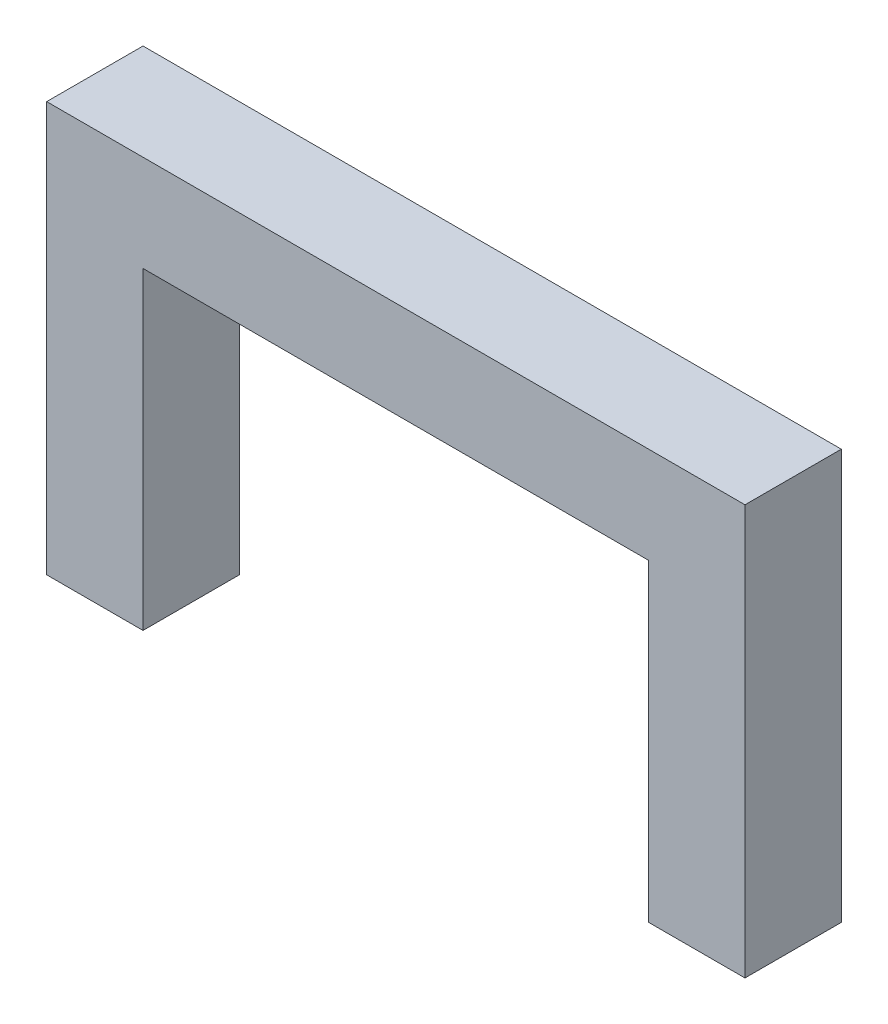
SolidWorks part; units mm, degrees
ref_plane "Front Plane" through (0, 0, 0) normal (0, 0, 1) x (1, 0, 0)
ref_plane "Top Plane" through (0, 0, 0) normal (0, 1, 0) x (1, 0, 0)
ref_plane "Right Plane" through (0, 0, 0) normal (1, 0, 0) x (0, 0, -1)
sketch "Sketch2" plane through (0, 0, 0) normal (0, 1, 0) x (1, 0, 0)
  line L0 (0, 0) -> (171.8553, 0) construction
  line L1 (0, 0) -> (19.05, 0)
  line L2 (0, 0) -> (0, -19.05)
  line L3 (0, -19.05) -> (19.05, -19.05)
  line L4 (19.05, 0) -> (19.05, -19.05)
  line L5 (0, -19.05) -> (171.8553, -19.05) construction
  line L7 (119.05, 0) -> (138.1, 0)
  line L8 (119.05, 0) -> (119.05, -19.05)
  line L9 (119.05, -19.05) -> (138.1, -19.05)
  line L10 (138.1, 0) -> (138.1, -19.05)
  dimension "D1" = 19.05
  dimension "D2" = 19.05
  dimension "D3" = 19.05
  dimension "D4" = 100
extrude "Boss-Extrude1" add sketch "Sketch2" along normal blind 62
sketch "Sketch3" plane through (0, 62, 0) normal (0, 1, 0) x (1, 0, 0)
  line L1 (0, 0) -> (138.1, 0)
  line L2 (0, 0) -> (0, -19.05)
  line L3 (0, -19.05) -> (138.1, -19.05)
  line L4 (138.1, 0) -> (138.1, -19.05)
extrude "Boss-Extrude2" add sketch "Sketch3" along normal blind 19.05
